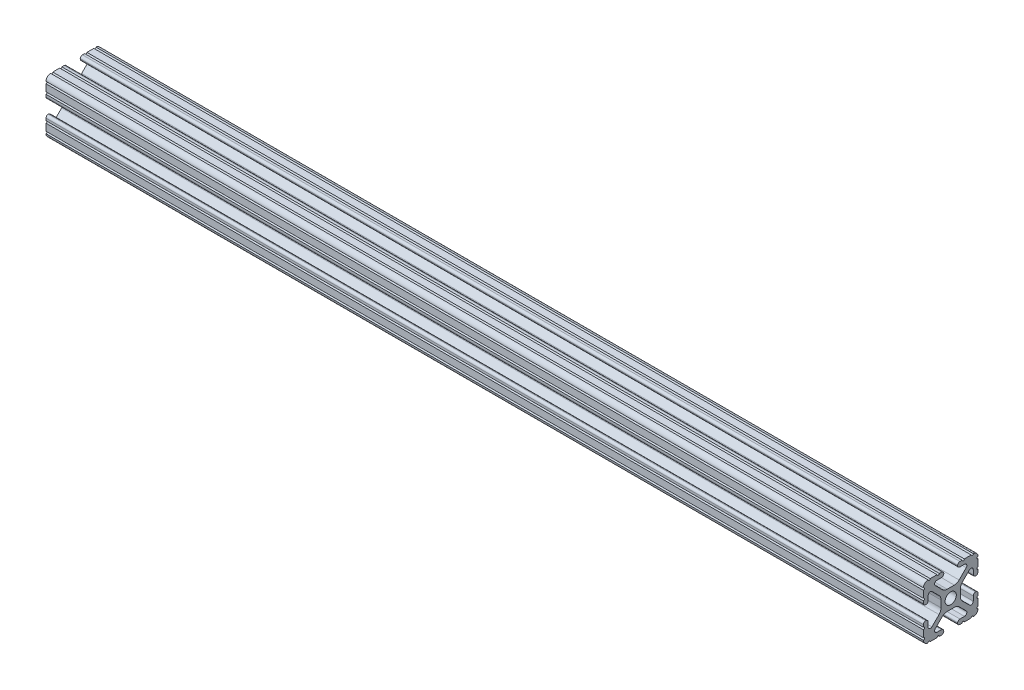
SolidWorks part; units mm, degrees
ref_plane "Front Plane" through (0, 0, 0) normal (0, 0, 1) x (1, 0, 0)
ref_plane "Top Plane" through (0, 0, 0) normal (0, 1, 0) x (1, 0, 0)
ref_plane "Right Plane" through (0, 0, 0) normal (1, 0, 0) x (0, 0, -1)
sketch "Sketch2" plane through (0, 0, 0) normal (0, 1, 0) x (1, 0, 0)
  line L0 (0, 0) -> (-408.432, 0)
  dimension "D1" = 408.432
other "10 1010 PROFILE(1)"
ref_plane "Plane1" through (0, 0, 0) normal (-1, 0, 0) x (0, 0, 1)
sketch "Sketch1" plane through (0, 0, 0) normal (-1, 0, 0) x (0, 0, 1)
  line L1 (12.7, 12.7) -> (-12.7, 12.7) construction
  line L2 (12.7, 12.7) -> (12.7, -12.7) construction
  line L3 (12.7, -12.7) -> (-12.7, -12.7) construction
  line L4 (-12.7, 12.7) -> (-12.7, -12.7) construction
  line L5 (12.7, 12.7) -> (-12.7, -12.7) construction
  line L6 (12.7, -12.7) -> (-12.7, 12.7) construction
  line L88 (-1.7093, -4.4958) -> (1.7093, -4.4958)
  line L89 (3.9523, -5.4237) -> (7.1797, -8.6452)
  line L90 (6.4164, -10.4902) -> (4.2875, -10.4902)
  line L91 (3.2385, -11.5392) -> (3.2385, -11.651)
  line L92 (4.2875, -12.7) -> (5.3171, -12.7)
  line L93 (6.3331, -12.7) -> (9.5504, -12.7)
  line L94 (12.7, -9.5504) -> (12.7, -6.3331)
  line L95 (12.7, -5.3171) -> (12.7, -4.2875)
  line L96 (11.651, -3.2385) -> (11.5392, -3.2385)
  line L97 (10.4902, -4.2875) -> (10.4902, -6.4021)
  line L98 (8.737, -7.1292) -> (5.4405, -3.8388)
  line L99 (4.5085, -1.5917) -> (4.5085, 1.5917)
  line L100 (5.4405, 3.8388) -> (8.737, 7.1292)
  line L101 (10.4902, 6.4021) -> (10.4902, 4.2875)
  line L102 (11.5392, 3.2385) -> (11.651, 3.2385)
  line L103 (12.7, 4.2875) -> (12.7, 5.3171)
  line L104 (12.7, 6.3331) -> (12.7, 9.5504)
  line L105 (9.5504, 12.7) -> (6.3331, 12.7)
  line L106 (5.3171, 12.7) -> (4.2875, 12.7)
  line L107 (3.2384, 11.651) -> (3.2384, 11.5392)
  line L108 (4.2875, 10.4902) -> (6.4768, 10.4902)
  line L109 (7.2072, 8.7245) -> (3.9003, 5.4237)
  line L110 (1.6573, 4.4958) -> (-1.6573, 4.4958)
  line L111 (-3.9003, 5.4237) -> (-7.2072, 8.7245)
  line L112 (-6.4768, 10.4902) -> (-4.2875, 10.4902)
  line L113 (-3.2384, 11.5392) -> (-3.2384, 11.651)
  line L114 (-4.2875, 12.7) -> (-5.3171, 12.7)
  line L115 (-6.3331, 12.7) -> (-9.5504, 12.7)
  line L116 (-12.7, 9.5504) -> (-12.7, 6.3331)
  line L117 (-12.7, 5.3171) -> (-12.7, 4.2875)
  line L118 (-11.651, 3.2385) -> (-11.5392, 3.2385)
  line L119 (-10.4902, 4.2875) -> (-10.4902, 6.4021)
  line L120 (-8.737, 7.1292) -> (-5.4405, 3.8388)
  line L121 (-4.5085, 1.5917) -> (-4.5085, -1.5917)
  line L122 (-5.4405, -3.8388) -> (-8.737, -7.1292)
  line L123 (-10.4902, -6.4021) -> (-10.4902, -4.2875)
  line L124 (-11.5392, -3.2385) -> (-11.651, -3.2385)
  line L125 (-12.7, -4.2875) -> (-12.7, -5.3171)
  line L126 (-12.7, -6.3331) -> (-12.7, -9.5504)
  line L127 (-9.5504, -12.7) -> (-6.3331, -12.7)
  line L128 (-5.3171, -12.7) -> (-4.2875, -12.7)
  line L129 (-3.2385, -11.651) -> (-3.2385, -11.5392)
  line L130 (-4.2875, -10.4902) -> (-6.4164, -10.4902)
  line L131 (-7.1797, -8.6452) -> (-3.9523, -5.4237)
  circle A1 centre (0, 0) radius 2.6035
  arc A104 (-1.7093, -4.4958) -> (-3.9523, -5.4237) centre (-1.7093, -7.6708) ccw
  arc A105 (3.9523, -5.4237) -> (1.7093, -4.4958) centre (1.7093, -7.6708) ccw
  arc A106 (6.4164, -10.4902) -> (7.1797, -8.6452) centre (6.4164, -9.4098) ccw
  arc A107 (4.2875, -10.4902) -> (3.2385, -11.5392) centre (4.2875, -11.5392) ccw
  arc A108 (3.2385, -11.651) -> (4.2875, -12.7) centre (4.2875, -11.651) ccw
  arc A109 (6.3331, -12.7) -> (5.3171, -12.7) centre (5.8251, -12.7) ccw
  arc A110 (10.5664, -12.6998) -> (9.5504, -12.7) centre (10.0584, -12.7) ccw
  arc A111 (10.5664, -12.6998) -> (12.6998, -10.5664) centre (10.5918, -10.5918) ccw
  arc A112 (12.7, -9.5504) -> (12.6998, -10.5664) centre (12.7, -10.0584) ccw
  arc A113 (12.7, -5.3171) -> (12.7, -6.3331) centre (12.7, -5.8251) ccw
  arc A114 (12.7, -4.2875) -> (11.651, -3.2385) centre (11.651, -4.2875) ccw
  arc A115 (11.5392, -3.2385) -> (10.4902, -4.2875) centre (11.5392, -4.2875) ccw
  arc A116 (8.737, -7.1292) -> (10.4902, -6.4021) centre (9.4628, -6.4021) ccw
  arc A117 (4.5085, -1.5917) -> (5.4405, -3.8388) centre (7.6835, -1.5917) ccw
  arc A118 (5.4405, 3.8388) -> (4.5085, 1.5917) centre (7.6835, 1.5917) ccw
  arc A119 (10.4902, 6.4021) -> (8.737, 7.1292) centre (9.4628, 6.4021) ccw
  arc A120 (10.4902, 4.2875) -> (11.5392, 3.2385) centre (11.5392, 4.2875) ccw
  arc A121 (11.651, 3.2385) -> (12.7, 4.2875) centre (11.651, 4.2875) ccw
  arc A122 (12.7, 6.3331) -> (12.7, 5.3171) centre (12.7, 5.8251) ccw
  arc A123 (12.6998, 10.5664) -> (12.7, 9.5504) centre (12.7, 10.0584) ccw
  arc A124 (12.6998, 10.5664) -> (10.5664, 12.6998) centre (10.5918, 10.5918) ccw
  arc A125 (9.5504, 12.7) -> (10.5664, 12.6998) centre (10.0584, 12.7) ccw
  arc A126 (5.3171, 12.7) -> (6.3331, 12.7) centre (5.8251, 12.7) ccw
  arc A127 (4.2875, 12.7) -> (3.2384, 11.651) centre (4.2875, 11.651) ccw
  arc A128 (3.2384, 11.5392) -> (4.2875, 10.4902) centre (4.2875, 11.5392) ccw
  arc A129 (7.2072, 8.7245) -> (6.4768, 10.4902) centre (6.4768, 9.4563) ccw
  arc A130 (1.6573, 4.4958) -> (3.9003, 5.4237) centre (1.6573, 7.6708) ccw
  arc A131 (-3.9003, 5.4237) -> (-1.6573, 4.4958) centre (-1.6573, 7.6708) ccw
  arc A132 (-6.4768, 10.4902) -> (-7.2072, 8.7245) centre (-6.4768, 9.4563) ccw
  arc A133 (-4.2875, 10.4902) -> (-3.2384, 11.5392) centre (-4.2875, 11.5392) ccw
  arc A134 (-3.2384, 11.651) -> (-4.2875, 12.7) centre (-4.2875, 11.651) ccw
  arc A135 (-6.3331, 12.7) -> (-5.3171, 12.7) centre (-5.8251, 12.7) ccw
  arc A136 (-10.5664, 12.6998) -> (-9.5504, 12.7) centre (-10.0584, 12.7) ccw
  arc A137 (-10.5664, 12.6998) -> (-12.6998, 10.5664) centre (-10.5918, 10.5918) ccw
  arc A138 (-12.7, 9.5504) -> (-12.6998, 10.5664) centre (-12.7, 10.0584) ccw
  arc A139 (-12.7, 5.3171) -> (-12.7, 6.3331) centre (-12.7, 5.8251) ccw
  arc A140 (-12.7, 4.2875) -> (-11.651, 3.2385) centre (-11.651, 4.2875) ccw
  arc A141 (-11.5392, 3.2385) -> (-10.4902, 4.2875) centre (-11.5392, 4.2875) ccw
  arc A142 (-8.737, 7.1292) -> (-10.4902, 6.4021) centre (-9.4628, 6.4021) ccw
  arc A143 (-4.5085, 1.5917) -> (-5.4405, 3.8388) centre (-7.6835, 1.5917) ccw
  arc A144 (-5.4405, -3.8388) -> (-4.5085, -1.5917) centre (-7.6835, -1.5917) ccw
  arc A145 (-10.4902, -6.4021) -> (-8.737, -7.1292) centre (-9.4628, -6.4021) ccw
  arc A146 (-10.4902, -4.2875) -> (-11.5392, -3.2385) centre (-11.5392, -4.2875) ccw
  arc A147 (-11.651, -3.2385) -> (-12.7, -4.2875) centre (-11.651, -4.2875) ccw
  arc A148 (-12.7, -6.3331) -> (-12.7, -5.3171) centre (-12.7, -5.8251) ccw
  arc A149 (-12.6998, -10.5664) -> (-12.7, -9.5504) centre (-12.7, -10.0584) ccw
  arc A150 (-12.6998, -10.5664) -> (-10.5664, -12.6998) centre (-10.5918, -10.5918) ccw
  arc A151 (-9.5504, -12.7) -> (-10.5664, -12.6998) centre (-10.0584, -12.7) ccw
  arc A152 (-5.3171, -12.7) -> (-6.3331, -12.7) centre (-5.8251, -12.7) ccw
  arc A153 (-4.2875, -12.7) -> (-3.2385, -11.651) centre (-4.2875, -11.651) ccw
  arc A154 (-3.2385, -11.5392) -> (-4.2875, -10.4902) centre (-4.2875, -11.5392) ccw
  arc A155 (-7.1797, -8.6452) -> (-6.4164, -10.4902) centre (-6.4164, -9.4098) ccw
  point P3 (0, 0)
  point P21 (-12.7, 0)
  point P22 (0, 12.7)
  point P25 (12.7, 0)
  point P28 (0, -12.7)
  point P30 (-12.7, -12.7)
  point P33 (12.7, -12.7)
  point P37 (12.7, 12.7)
  point P40 (-12.7, 12.7)
  point P43 (0, 0)
  dimension "D1" = 25.4
sketch "Sketch3" plane through (0, 4.4958, 0) normal (0, 1, 0) x (1, 0, 0)
  line L0 (0, 0) -> (-408.432, 0) construction
  point P0 (-33.274, 0)
  point P1 (-60.198, 0)
  point P4 (-84.074, 0)
  point P5 (-214.122, 0)
  point P6 (-240.792, 0)
  point P7 (-370.586, 0)
  dimension "D1" = 33.274
  dimension "D2" = 60.198
  dimension "D3" = 84.074
  dimension "D4" = 214.122
  dimension "D5" = 240.792
  dimension "D6" = 370.586
sketch "Sketch5" plane through (0, 12.7, 0) normal (0, 1, 0) x (1, 0, 0)
  point P0 (-370.586, 0)
  point P1 (-240.792, 0)
  point P3 (-214.122, 0)
  point P5 (-84.074, 0)
  point P7 (-60.198, 0)
  point P9 (-33.274, 0)
hole_wizard "M6x1.0 Tapped Hole1" positions "3DSketch5" profile "Sketch9" tap size "M6x1.0" standard "ANSI Metric"
sketch3d "3DSketch5"
  line L0 (-408.432, 4.4958, 1.6573) -> (0, 4.4958, 1.6573) construction
  point P0 (-33.1174, 4.4958, 1.6573)
  point P4 (-60.198, 12.7, 0)
  point P7 (-84.074, 12.7, 0)
  point P10 (-214.122, 12.7, 0)
  point P13 (-240.792, 12.7, 0)
  point P16 (-370.586, 12.7, 0)
sketch "Sketch9" plane through (-370.586, 12.7, 0) normal (1, 0, 0) x (0, 0, 1)
  line L0 (0, 0) -> (0, 25.4)
  line L1 (0, 25.4) -> (2.5, 25.4)
  line L2 (2.5, 25.4) -> (2.5, 0)
  line L5 (2.5, 0) -> (0, 0)
  line L11 (0, -6.35) -> (0, 107.95) construction
  dimension "Thru Tap Drill Dia." = 5
  dimension "Thru Tap Drill Depth" = 25.4
cosmetic thread "Hole Thread1" parameters "D2"=6
cosmetic thread "Hole Thread2" parameters "D2"=6
cosmetic thread "Hole Thread3" parameters "D2"=6
cosmetic thread "Hole Thread4" parameters "D2"=6
cosmetic thread "Hole Thread5" parameters "D2"=6
cosmetic thread "Hole Thread6" parameters "D2"=6
hole_wizard "M6x1.0 Tapped Hole2" positions "3DSketch6" profile "Sketch10" tap size "M6x1.0" standard "ANSI Metric" end condition through all
sketch3d "3DSketch6"
  point P0 (-33.274, 12.7, 0)
sketch "Sketch10" plane through (-33.274, 12.7, 0) normal (1, 0, 0) x (0, 0, 1)
  line L0 (0, 0) -> (0, 25.4)
  line L1 (0, 25.4) -> (2.5, 25.4)
  line L2 (2.5, 25.4) -> (2.5, 0)
  line L5 (2.5, 0) -> (0, 0)
  line L11 (0, -6.35) -> (0, 107.95) construction
  dimension "Thru Tap Drill Dia." = 5
  dimension "Thru Tap Drill Depth" = 25.4
cosmetic thread "Hole Thread7" parameters "D2"=6
